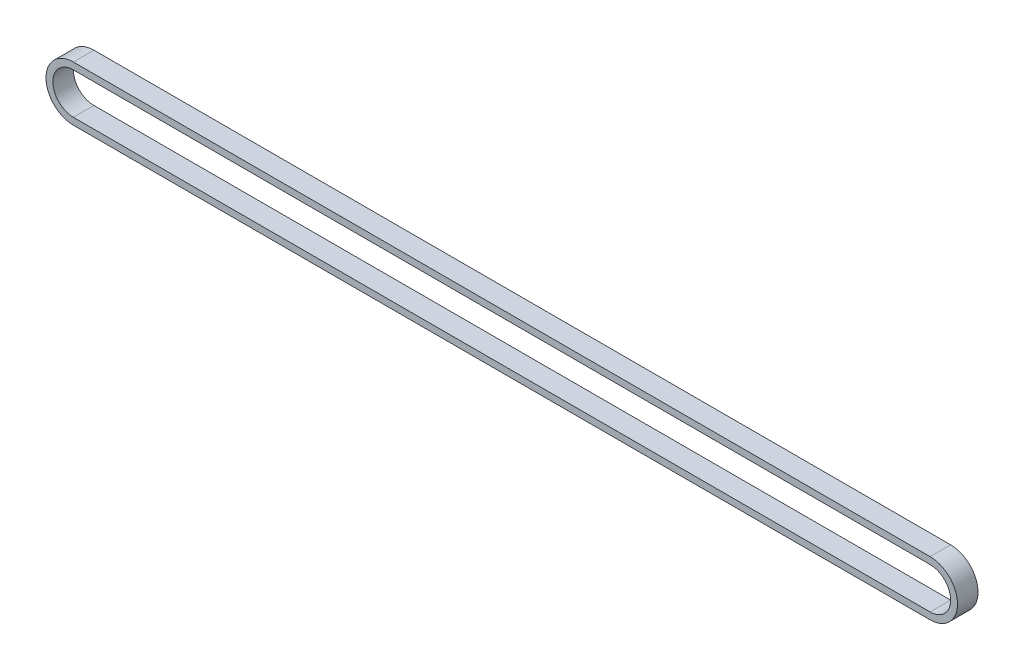
SolidWorks part; units mm, degrees
ref_plane "Plano frontal" through (0, 0, 0) normal (0, 0, 1) x (1, 0, 0)
ref_plane "Plano superior" through (0, 0, 0) normal (0, 1, 0) x (1, 0, 0)
ref_plane "Plano direito" through (0, 0, 0) normal (1, 0, 0) x (0, 0, -1)
sketch "Esboço1" plane through (0, 0, 0) normal (0, 0, 1) x (1, 0, 0)
  line L0 (-125.25, 0) -> (125.25, 0) construction
  line L1 (-125.25, 6) -> (125.25, 6)
  line L2 (-125.25, -6) -> (125.25, -6)
  line L3 (-125.25, 8) -> (125.25, 8)
  line L4 (-125.25, -8) -> (125.25, -8)
  arc A0 (-125.25, 6) -> (-125.25, -6) centre (-125.25, 0) ccw
  arc A1 (125.25, -6) -> (125.25, 6) centre (125.25, 0) ccw
  arc A2 (125.25, -8) -> (125.25, 8) centre (125.25, 0) ccw
  arc A3 (-125.25, 8) -> (-125.25, -8) centre (-125.25, 0) ccw
  point P2 (0, 0)
  dimension "D2" = 6
  dimension "D1" = 250.5
  dimension "D3" = 2
extrude "Ressalto-extrusão1" add sketch "Esboço1" along normal blind 6
